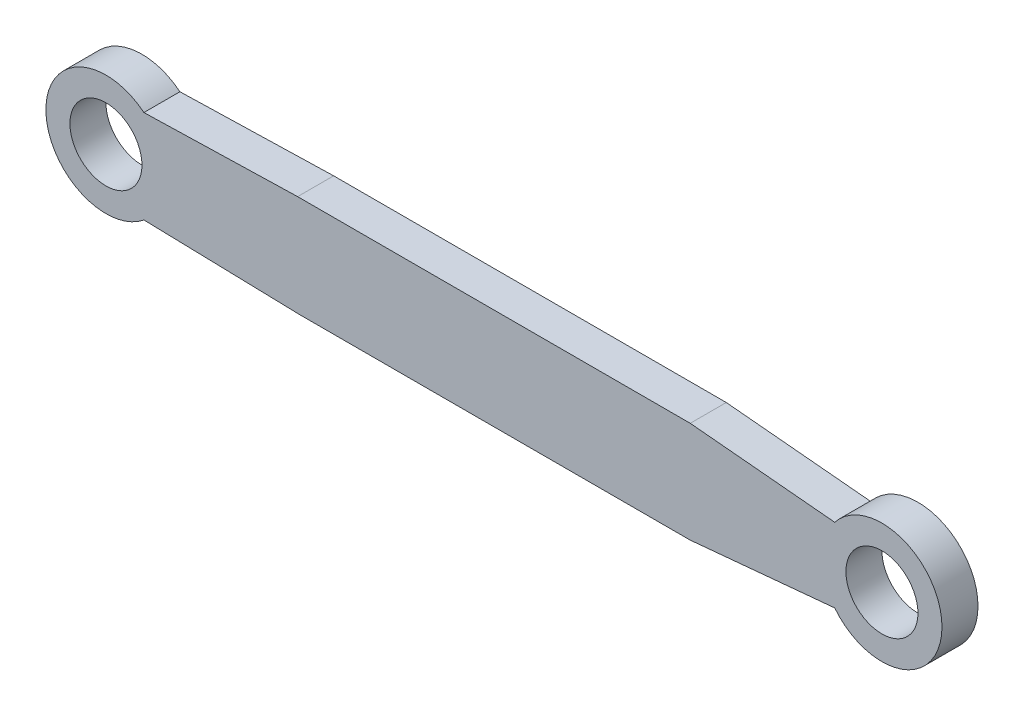
SolidWorks part; units mm, degrees
ref_plane "Front Plane" through (0, 0, 0) normal (0, 0, 1) x (1, 0, 0)
ref_plane "Top Plane" through (0, 0, 0) normal (0, 1, 0) x (1, 0, 0)
ref_plane "Right Plane" through (0, 0, 0) normal (1, 0, 0) x (0, 0, -1)
sketch "Sketch1" plane through (0, 0, 0) normal (0, 0, 1) x (1, 0, 0)
  line L0 (-323.1176, 0) -> (0, 0) construction
  line L1 (0, 0) -> (323.1176, 0) construction
  line L2 (-163.4801, 42.1145) -> (0, 42.1145)
  line L3 (0, 42.1145) -> (163.4801, 42.1145)
  line L4 (-163.4801, 42.1145) -> (-161.5588, 0) construction
  line L5 (-161.5588, 0) -> (-161.5588, -42.1583) construction
  line L6 (-161.5588, -42.1583) -> (163.4801, -42.1583)
  line L7 (163.4801, -42.1583) -> (283.7995, -30.8883)
  line L8 (163.4801, 42.1145) -> (283.7995, 30.8883)
  line L9 (-163.4801, 42.1145) -> (-291.5062, 38.7391)
  line L10 (-161.5588, -42.1583) -> (-291.5062, -38.7391)
  circle A0 centre (-323.1176, 0) radius 50
  circle A1 centre (-323.1176, 0) radius 30
  circle A2 centre (323.1176, 0) radius 50
  circle A3 centre (323.1176, 0) radius 30
  point P10 (273.8061, 38.7391)
  point P19 (276.6932, -38.7391)
  point P20 (0, 0)
  point P21 (273.8061, -38.7391)
  dimension "D1" = 646.2352
  dimension "D2" = 60
  dimension "D3" = 100
  dimension "D4" = 60
  dimension "D5" = 100
extrude "Boss-Extrude1" add sketch "Sketch1" along normal blind 30 contours A0 A1 | A2 L8 L3 L2 L9 A0 L10 L6 L7 | A2 A3
